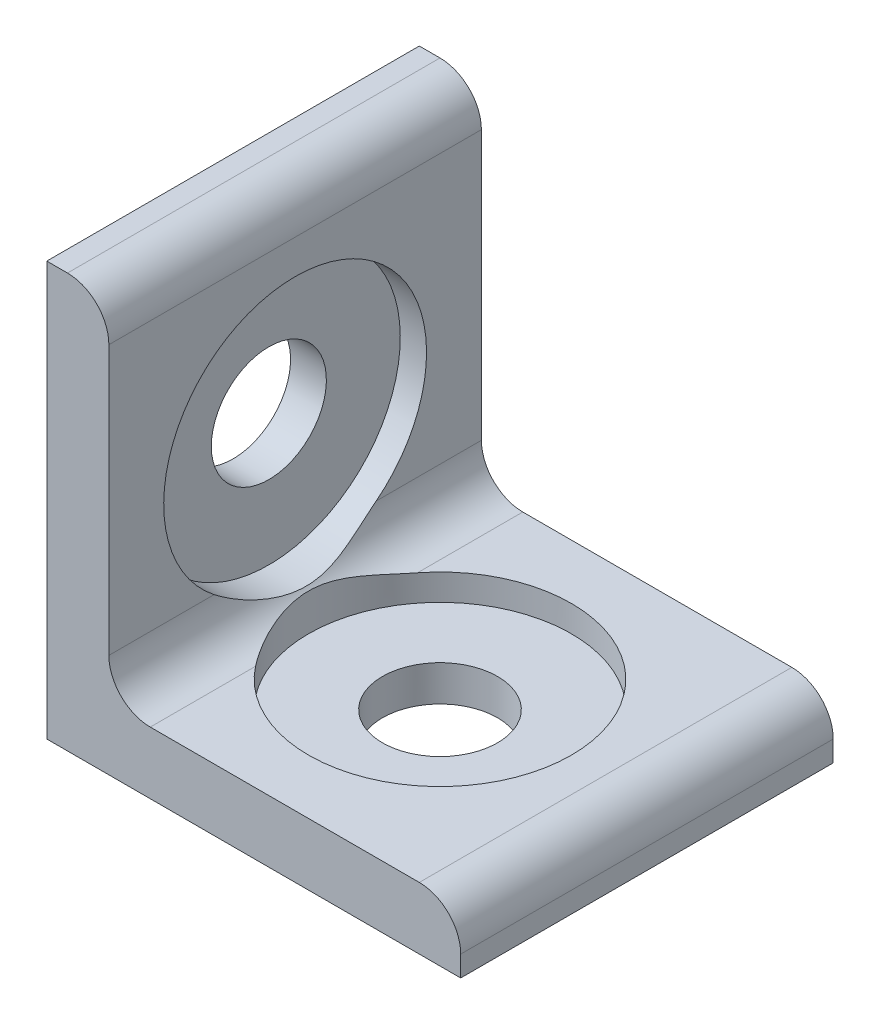
SolidWorks part; units mm, degrees
material "6061 Alloy"
ref_plane "Front" through (0, 0, 0) normal (0, 0, 1) x (1, 0, 0)
ref_plane "Top" through (0, 0, 0) normal (0, 1, 0) x (1, 0, 0)
ref_plane "Right" through (0, 0, 0) normal (1, 0, 0) x (0, 0, -1)
sketch "Sketch1" plane through (0, 0, 0) normal (0, 0, 1) x (1, 0, 0)
  line L1 (0, 0) -> (20, 0)
  line L2 (0, 0) -> (0, 20)
  line L3 (0, 20) -> (1, 20)
  line L4 (20, 0) -> (20, 1)
  line L7 (18, 3) -> (5, 3)
  line L8 (3, 18) -> (3, 5)
  arc A0 (5, 3) -> (3, 5) centre (5, 5) cw
  arc A1 (20, 1) -> (18, 3) centre (18, 1) ccw
  arc A2 (1, 20) -> (3, 18) centre (1, 18) cw
  point P13 (3, 20)
  dimension "D1" = 2
  dimension "D4" = 2
  dimension "D2" = 20
  dimension "D3" = 3
extrude "Boss-Extrude1" add sketch "Sketch1" along normal mid plane 18
sketch "Sketch2" plane through (0, 0, 0) normal (0, -1, 0) x (-1, 0, 0)
  circle A0 centre (-10, 0) radius 2.78
  dimension "D2" = 0
  dimension "D4" = 5.56
extrude "Cut-Extrude1" cut sketch "Sketch2" against normal through all
sketch "Sketch3" plane through (0, 0, 0) normal (-1, 0, 0) x (0, 0, 1)
  circle A0 centre (0, 10) radius 2.78
  dimension "D4" = 5.56
  dimension "D2" = 0
extrude "Cut-Extrude2" cut sketch "Sketch3" against normal through all
sketch "Sketch6" plane through (3, 0, 0) normal (1, 0, 0) x (0, 0, -1)
  circle A0 centre (0, 10) radius 6.35
  dimension "D1" = 12.7
extrude "Cut-Extrude3" cut sketch "Sketch6" against normal blind 1.27 and the other way through all
sketch "Sketch7" plane through (0, 3, 0) normal (0, 1, 0) x (1, 0, 0)
  circle A0 centre (10, 0) radius 6.35
  dimension "D1" = 12.7
extrude "Cut-Extrude4" cut sketch "Sketch7" against normal blind 1.27 and the other way through all
